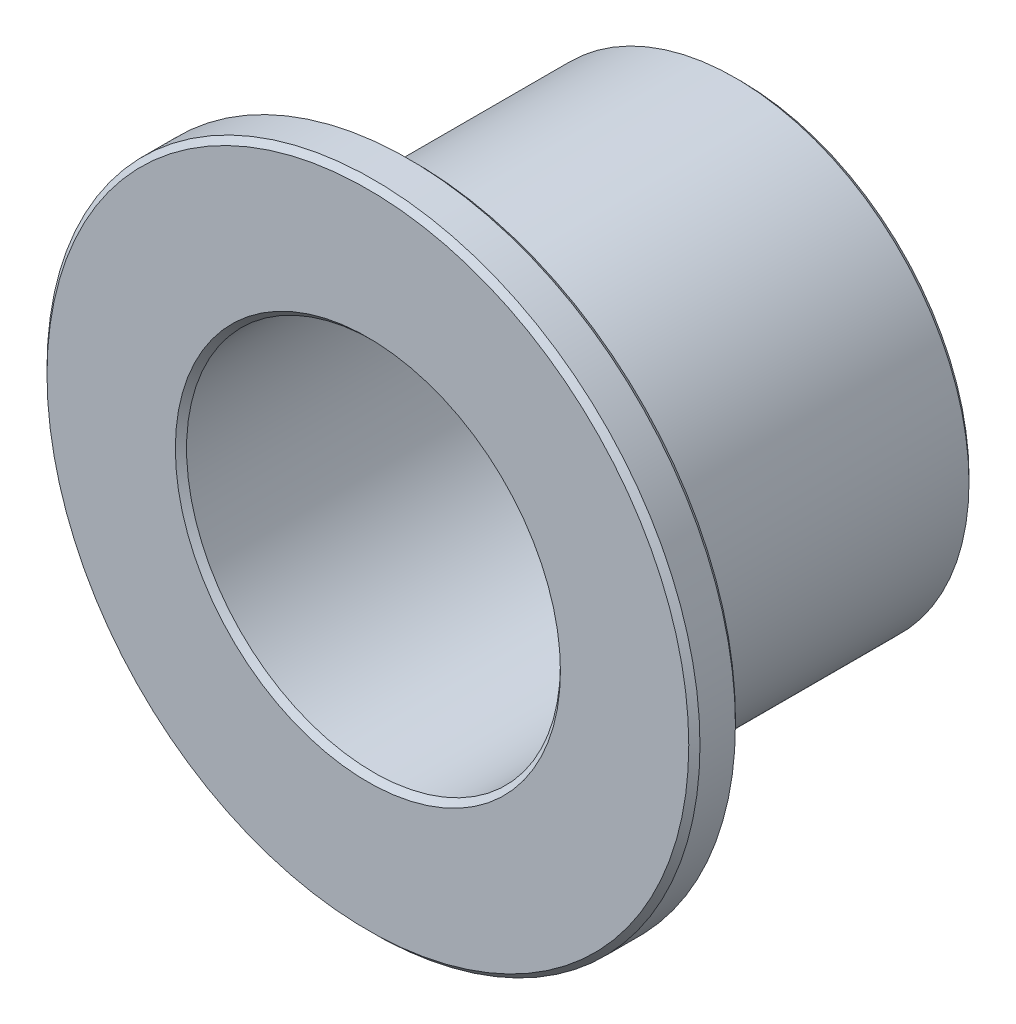
SolidWorks part; units mm, degrees
material "AISI Type A2 Tool Steel"
ref_plane "Front" through (0, 0, 0) normal (0, 0, 1) x (1, 0, 0)
ref_plane "Top" through (0, 0, 0) normal (0, 1, 0) x (1, 0, 0)
ref_plane "Right" through (0, 0, 0) normal (1, 0, 0) x (0, 0, -1)
sketch "Sketch1" plane through (0, 0, 0) normal (0, 0, 1) x (1, 0, 0)
  circle A0 centre (0, 0) radius 6.3627
  circle A1 centre (0, 0) radius 7.9502
  circle A2 centre (0, 0) radius 11.1125
  dimension "ID" = 12.7254
  dimension "OD" = 15.9004
  dimension "Flange OD" = 22.225
sketch "Sketch2" plane through (0, 0, 0) normal (1, 0, 0) x (0, 0, -1)
  line L0 (-6.35, -11.1125) -> (6.35, -11.1125) construction
  line L1 (0, 11.1125) -> (0, -11.1125) construction
  line L3 (-4.7625, 7.9502) -> (6.35, 7.9502) construction
  point P3 (0, -11.1125)
  point P7 (0, 7.9502)
  point P9 (-4.7625, -11.1125)
  point P10 (-6.35, 11.1125)
  point P23 (0, 11.1125)
  dimension "Flange Thickness" = 1.5875
  dimension "Length" = 12.7
sketch "Sketch3" plane through (0, 0, 0) normal (0, 0, 1) x (1, 0, 0)
  circle A0 centre (0, 0) radius 11.1125 construction
  circle A1 centre (0, 0) radius 11.1125
  circle A2 centre (0, 0) radius 6.3627 construction
  circle A3 centre (0, 0) radius 6.3627
extrude "Boss-Extrude1" add sketch "Sketch3" against normal up to vertex (-4.7625 mm away) from vertex at 6.35 starting at point (0, -11.1125, 6.35)
sketch "Sketch4" plane through (0, 0, 0) normal (0, 0, 1) x (1, 0, 0)
  circle A0 centre (0, 0) radius 6.3627 construction
  circle A1 centre (0, 0) radius 7.9502 construction
  circle A2 centre (0, 0) radius 6.3627
  circle A3 centre (0, 0) radius 7.9502
extrude "Boss-Extrude2" add sketch "Sketch4" against normal up to vertex (6.35 mm away) from vertex at 4.7625 starting at point (0, -11.1125, 4.7625)
chamfer "Chamfer1" distance 0.1909 angle 45 6 edges at (6.3627, 0, 6.35) (11.1125, 0, 6.35) (11.1125, 0, 4.7625) (7.9502, 0, 4.7625) (6.3627, 0, -6.35) (7.9502, 0, -6.35)
equation "\"D1@Chamfer1\"=\"ID@Sketch1\"*0.015"
